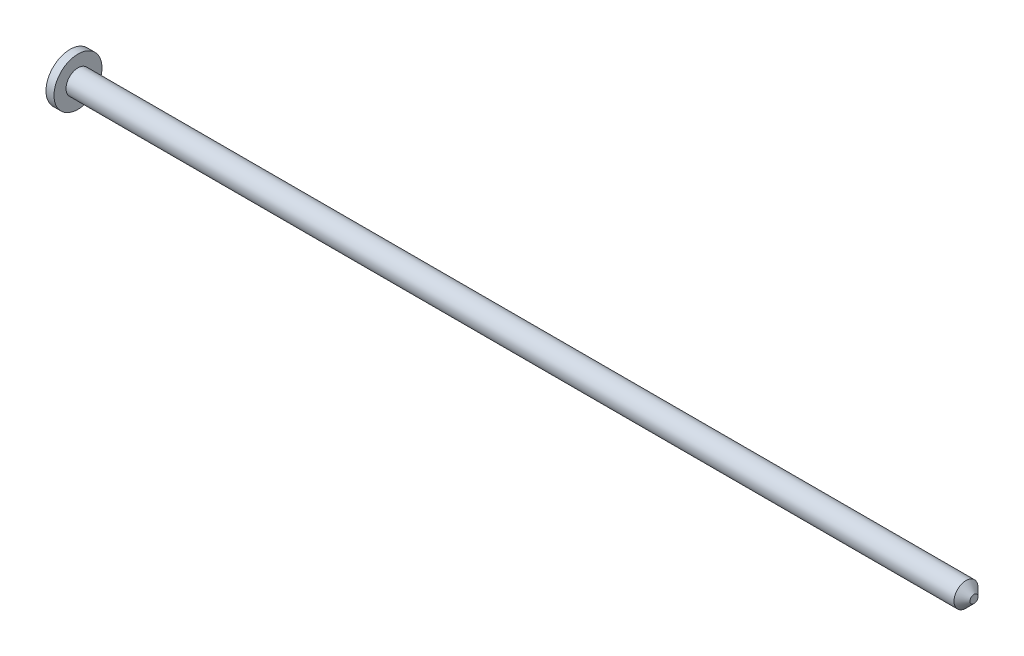
SolidWorks part; units mm, degrees
ref_plane "Front Plane" through (0, 0, 0) normal (0, 0, 1) x (1, 0, 0)
ref_plane "Top Plane" through (0, 0, 0) normal (0, 1, 0) x (1, 0, 0)
ref_plane "Right Plane" through (0, 0, 0) normal (1, 0, 0) x (0, 0, -1)
sketch "Sketch1" plane through (0, 0, 0) normal (0, 0, 1) x (1, 0, 0)
  line L0 (0, 0) -> (113, 0)
  line L1 (113, 0) -> (113, 1.5)
  line L2 (113, 1.5) -> (1, 1.5)
  line L4 (0, 3) -> (0, 0)
  line L5 (0, 3) -> (1, 3)
  line L6 (1, 3) -> (1, 1.5)
  dimension "D1" = 113
  dimension "D2" = 1.5
  dimension "D3" = 3
  dimension "D4" = 1
revolve "Revolve1" add sketch "Sketch1" angle 360 about L0
cosmetic thread "Cosmetic Thread1" parameters "D1"=7, "D2"=2.9
chamfer "Chamfer1" distance 1 angle 45 1 edges at (113, 0, 1.5)
